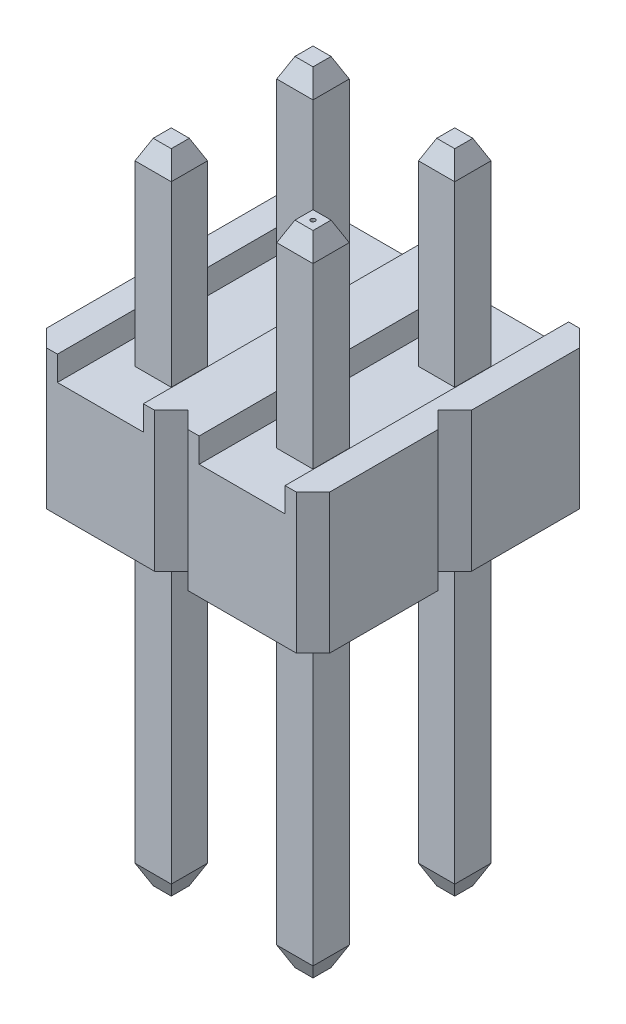
SolidWorks part; units mm, degrees
ref_plane "Front Plane" through (0, 0, 0) normal (0, 0, 1) x (1, 0, 0)
ref_plane "Top Plane" through (0, 0, 0) normal (0, 1, 0) x (1, 0, 0)
ref_plane "Right Plane" through (0, 0, 0) normal (1, 0, 0) x (0, 0, -1)
sketch "Sketch1" plane through (0, 0, 0) normal (0, 1, 0) x (1, 0, 0)
  line L0 (-0.97, 1.27) -> (0.97, 1.27)
  line L5 (0.97, 1.27) -> (1.27, 0.97)
  line L6 (1.27, 0.97) -> (1.27, -0.97)
  line L7 (1.27, -0.97) -> (0.97, -1.27)
  line L8 (0.97, -1.27) -> (-0.97, -1.27)
  line L9 (-0.97, -1.27) -> (-1.27, -0.97)
  line L10 (-1.27, -0.97) -> (-1.27, 0.97)
  line L11 (-1.27, 0.97) -> (-0.97, 1.27)
  dimension "D5" = 0.97
  dimension "D6" = 0.97
  dimension "D7" = 0.97
  dimension "D8" = 0.97
extrude "Extrude1" add sketch "Sketch1" along normal blind 2.5
sketch "Sketch2" plane through (0, 0, 1.27) normal (0, 0, 1) x (1, 0, 0)
  line L0 (-0.97, 0) -> (0.97, 0) construction
  line L1 (-0.77, 2.5687) -> (0.77, 2.5687)
  line L2 (-0.77, 2.5687) -> (-0.77, 2.06)
  line L3 (-0.77, 2.06) -> (0.77, 2.06)
  line L4 (0.77, 2.5687) -> (0.77, 2.06)
  dimension "D1" = 0.77
  dimension "D2" = 0.77
  dimension "D3" = 2.06
extrude "Cut-Extrude1" cut sketch "Sketch2" against normal blind 12.5
sketch "Sketch3" plane through (0, 2.06, 0) normal (0, 1, 0) x (-1, 0, 0)
  line L1 (0.325, -0.325) -> (-0.325, -0.325)
  line L2 (0.325, -0.325) -> (0.325, 0.325)
  line L3 (0.325, 0.325) -> (-0.325, 0.325)
  line L4 (-0.325, -0.325) -> (-0.325, 0.325)
  dimension "D1" = 0.65
  dimension "D2" = 0.325
  dimension "D3" = 0.65
  dimension "D4" = 0.325
extrude "Extrude2" add sketch "Sketch3" along normal blind 3.54
chamfer "Chamfer1" distance 0.35 angle 25 4 edges at (0, 5.6, -0.325) (0.325, 5.6, 0) (0, 5.6, 0.325) (-0.325, 5.6, 0)
sketch "Sketch4" plane through (0, 0, 0) normal (0, -1, 0) x (1, 0, 0)
  line L1 (-0.325, 0.325) -> (0.325, 0.325)
  line L2 (-0.325, 0.325) -> (-0.325, -0.325)
  line L3 (-0.325, -0.325) -> (0.325, -0.325)
  line L4 (0.325, 0.325) -> (0.325, -0.325)
extrude "Extrude3" add sketch "Sketch4" along normal blind 6
chamfer "Chamfer2" distance 0.35 angle 25 4 edges at (0, -6, 0.325) (0.325, -6, 0) (0, -6, -0.325) (-0.325, -6, 0)
pattern_linear "LPattern3" count 2 spacing 2.54 along (0, 0, -1) count 2 spacing 2.54 along (-1, 0, 0) of "Extrude1", "Cut-Extrude1"
pattern_linear "LPattern4" count 2 spacing 2.54 along (0, 0, -1) count 2 spacing 2.54 along (-1, 0, 0) of "Extrude2", "Chamfer1", "Extrude3", "Chamfer2"
sketch "Esboço1" plane through (0, 5.6, 0) normal (0, 1, 0) x (1, 0, 0)
  circle A0 centre (0, 0) radius 0.0396
extrude "Corte-extrusão1" cut sketch "Esboço1" against normal blind 0.1
